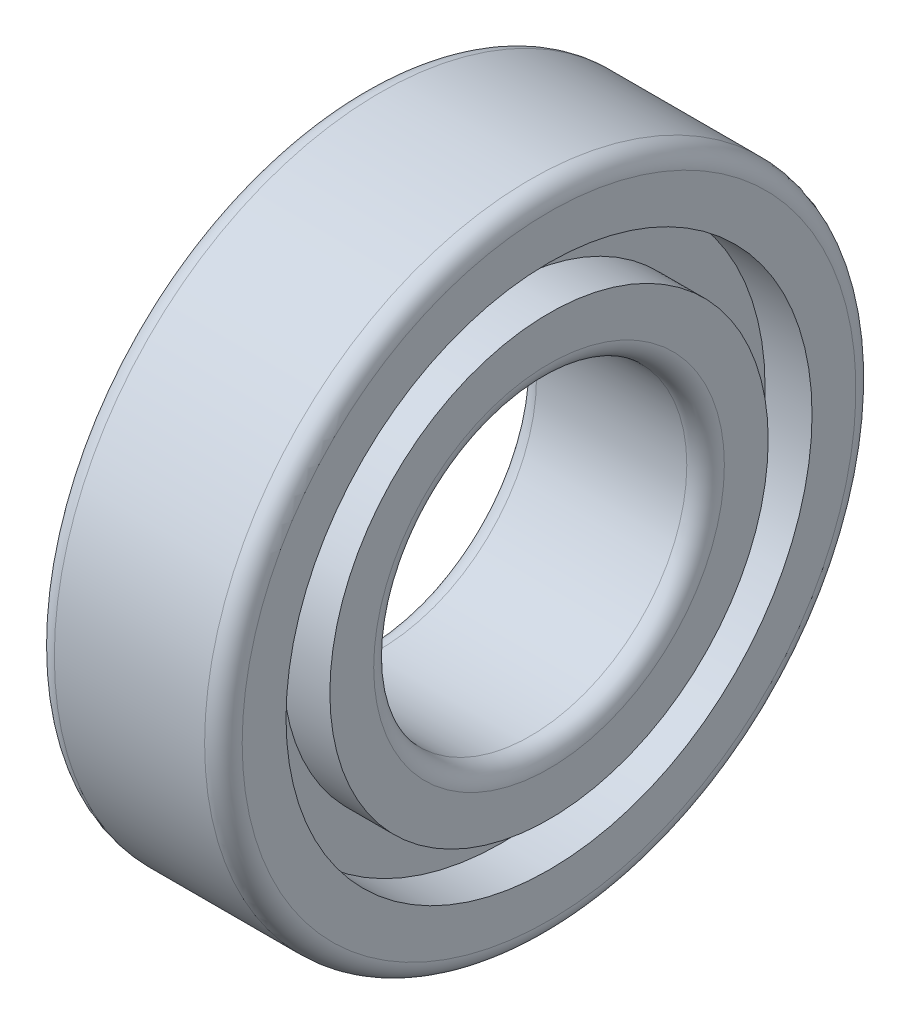
SolidWorks part; units mm, degrees
material "AISI 1020"
ref_plane "Спереди" through (0, 0, 0) normal (0, 0, 1) x (1, 0, 0)
ref_plane "Сверху" through (0, 0, 0) normal (0, 1, 0) x (1, 0, 0)
ref_plane "Справа" through (0, 0, 0) normal (1, 0, 0) x (0, 0, -1)
sketch "Эскиз1" plane through (0, 0, 0) normal (0, 0, 1) x (1, 0, 0)
  line L0 (6, 12.5) -> (-6, 12.5)
  line L1 (-7.5, 14) -> (-7.5, 17.5)
  line L2 (-7.5, 17.5) -> (-3.75, 17.5)
  line L3 (-3.75, 17.5) -> (-3.75, 21)
  line L4 (-3.75, 21) -> (-7.5, 21)
  line L5 (-7.5, 21) -> (-7.5, 24.5)
  line L6 (-6, 26) -> (6, 26)
  line L7 (-873.9917, 0) -> (42825.5954, 0) construction
  line L8 (0, -873.9917) -> (0, 42825.5954) construction
  line L9 (7.5, 21) -> (7.5, 24.5)
  line L10 (3.75, 21) -> (7.5, 21)
  line L11 (3.75, 17.5) -> (3.75, 21)
  line L12 (7.5, 17.5) -> (3.75, 17.5)
  line L13 (7.5, 14) -> (7.5, 17.5)
  arc A0 (-6, 12.5) -> (-7.5, 14) centre (-6, 14) cw
  arc A1 (-7.5, 24.5) -> (-6, 26) centre (-6, 24.5) cw
  arc A2 (7.5, 24.5) -> (6, 26) centre (6, 24.5) ccw
  arc A3 (6, 12.5) -> (7.5, 14) centre (6, 14) ccw
  point P25 (0, 26)
  point P29 (0, 12.5)
  dimension "D3" = 1.5
  dimension "B" = 15
  dimension "D1" = 25
  dimension "D2" = 52
  dimension "D4" = 3.75
revolve "Повернуть1" add sketch "Эскиз1" angle 360 about L7
equation "\"D4@Эскиз1\"=\"B@Эскиз1\"/4"
